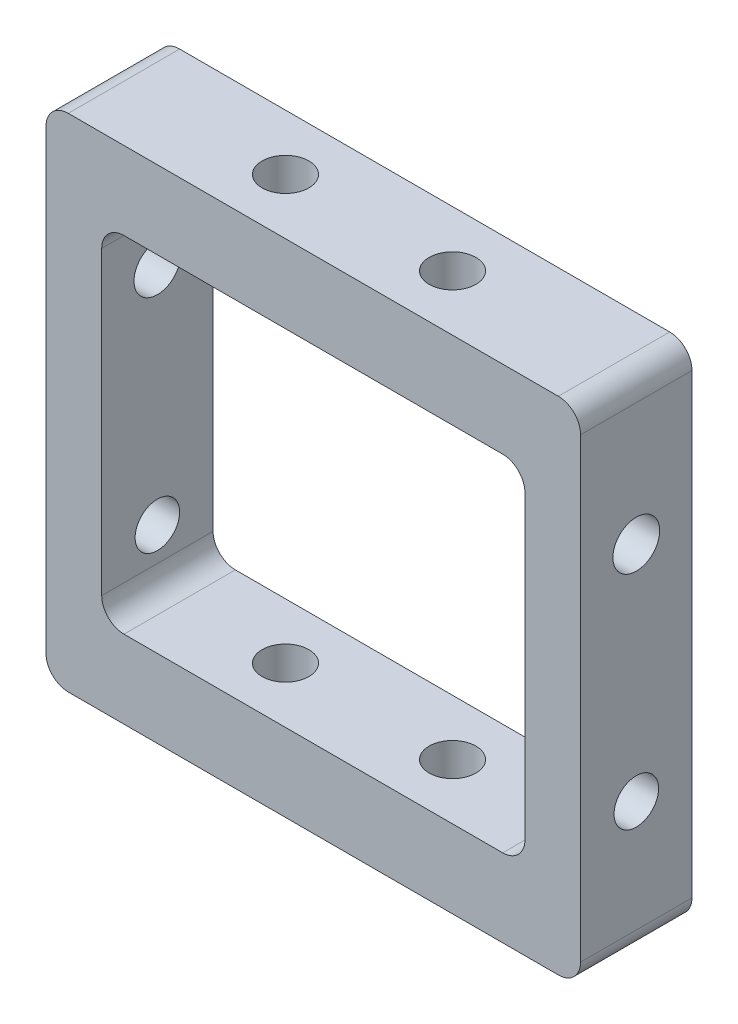
SolidWorks part; units mm, degrees
material "1060 合金"
ref_plane "前视基准面" through (0, 0, 0) normal (0, 0, 1) x (1, 0, 0)
ref_plane "上视基准面" through (0, 0, 0) normal (0, 1, 0) x (1, 0, 0)
ref_plane "右视基准面" through (0, 0, 0) normal (1, 0, 0) x (0, 0, -1)
sketch "草图1" plane through (0, 0, 0) normal (0, 0, 1) x (1, 0, 0)
  line L1 (-24, -22.5) -> (24, -22.5)
  line L2 (-24, -22.5) -> (-24, 22.5)
  line L3 (-24, 22.5) -> (24, 22.5)
  line L4 (24, -22.5) -> (24, 22.5)
  line L5 (-24, -22.5) -> (24, 22.5) construction
  line L6 (-24, 22.5) -> (24, -22.5) construction
  point P0 (0, 0)
  dimension "D1" = 45
  dimension "D2" = 48
extrude "凸台-拉伸1" add sketch "草图1" along normal blind 10
sketch "草图2" plane through (0, 22.5, 0) normal (0, 1, 0) x (1, 0, 0)
  line L0 (24, -5) -> (10, -5) construction
  line L1 (24, -10) -> (24, 0) construction
  line L2 (0, 0) -> (0, -13.6651) construction
  circle A0 centre (10, -5) radius 2.5
  circle A1 centre (-10, -5) radius 2.5
  dimension "D1" = 5
  dimension "D2" = 20
extrude "切除-拉伸1" cut sketch "草图2" against normal through all both and the other way through all
sketch "草图3" plane through (24, 0, 0) normal (1, 0, 0) x (0, 0, -1)
  line L0 (-5, -22.5) -> (-5, -10.5) construction
  line L1 (-10, -22.5) -> (0, -22.5) construction
  circle A0 centre (-5, -10.5) radius 2
  dimension "D1" = 4
  dimension "D2" = 12
extrude "切除-拉伸2" cut sketch "草图3" against normal through all
sketch "草图4" plane through (24, 0, 0) normal (1, 0, 0) x (0, 0, -1)
  line L0 (-5, -10.5) -> (-5, 9.5) construction
  circle A0 centre (-5, 9.5) radius 1.75
  dimension "D2" = 3.5
  dimension "D1" = 20
extrude "切除-拉伸3" cut sketch "草图4" against normal through all both and the other way through all
sketch "草图5" plane through (0, 0, 10) normal (0, 0, 1) x (1, 0, 0)
  line L0 (-8.15, -8.5) -> (-12.15, -8.5) construction
  line L1 (-12.5, -8.5) -> (-24, -8.5) construction
  line L3 (-10.15, -8.5) -> (-10.15, -12.5) construction
  line L4 (-10.15, -12.5) -> (-7.5, -12.5) construction
  line L6 (-10.15, -10.5) -> (24, -10.5) construction
  line L7 (-12.15, 8.15) -> (-8.15, 8.15) construction
  line L9 (-10.15, 8.15) -> (-10.15, 10.85) construction
  line L10 (-10.15, 10.85) -> (-7.85, 10.85) construction
  line L12 (-10.15, 9.5) -> (24, 9.5) construction
  line L13 (24, -22.5) -> (24, 22.5) construction
  line L14 (12.15, 8.15) -> (7.85, 8.15) construction
  line L16 (10, 8.15) -> (10, 9.5) construction
  line L17 (12.5, -8.5) -> (9.85, -8.5) construction
  line L18 (9.85, -8.5) -> (9.85, -10.5) construction
  line L19 (9.85, -8.5) -> (7.2, -8.5) construction
  line L20 (-24, -22.5) -> (24, -22.5) construction
  line L21 (-19, -2) -> (-1.3, -2)
  line L22 (-19, -2) -> (-19, -19)
  line L23 (-19, -19) -> (-1.3, -19)
  line L24 (-1.3, -2) -> (-1.3, -19)
  line L25 (-19, -2) -> (-1.3, -19) construction
  line L26 (-19, -19) -> (-1.3, -2) construction
  line L28 (0, 0) -> (0, -22.5) construction
  line L29 (19, -2) -> (1.3, -2)
  line L30 (1.3, -2) -> (1.3, -19)
  line L31 (19, -19) -> (1.3, -19)
  line L32 (19, -2) -> (19, -19)
  line L33 (24, 9.5) -> (24, -10.5) construction
  line L34 (24, -0.5) -> (0, -0.5) construction
  line L35 (-19, 18) -> (-1.3, 18)
  line L36 (-1.3, 1) -> (-1.3, 18)
  line L37 (-19, 1) -> (-1.3, 1)
  line L38 (-19, 1) -> (-19, 18)
  line L39 (19, 1) -> (19, 18)
  line L40 (19, 18) -> (1.3, 18)
  line L41 (1.3, 1) -> (1.3, 18)
  line L42 (19, 1) -> (1.3, 1)
  line L43 (-24, 22.5) -> (-24, -22.5) construction
  dimension "D1" = 2.65
  dimension "D2" = 5
  dimension "D3" = 3.5
  dimension "D4" = 20
  dimension "D5" = 2.65
extrude "切除-拉伸4" cut sketch "草图5" against normal through all
sketch "草图6" plane through (0, 0, 10) normal (0, 0, 1) x (1, 0, 0)
  line L0 (-19, 18) -> (-19, 16.5)
  line L1 (-19, 16.5) -> (-1.3, 16.5)
  line L2 (-1.3, 16.5) -> (-1.3, 18)
  line L3 (-1.3, 18) -> (-19, 18)
  line L4 (24, 22.5) -> (-24, 22.5) construction
  line L5 (0, 0) -> (0, 22.5) construction
  line L6 (1.3, 16.5) -> (1.3, 18)
  line L7 (19, 16.5) -> (1.3, 16.5)
  line L8 (19, 18) -> (19, 16.5)
  line L9 (1.3, 18) -> (19, 18)
  line L10 (-19, 1) -> (-19, -1.5)
  line L11 (-19, -1.5) -> (-1.3, -1.5)
  line L12 (-1.3, -1.5) -> (-1.3, 1)
  line L13 (-1.3, 1) -> (-19, 1)
  line L14 (1.3, -1.5) -> (1.3, 1)
  line L15 (19, -1.5) -> (1.3, -1.5)
  line L16 (19, 1) -> (19, -1.5)
  line L17 (1.3, 1) -> (19, 1)
  dimension "D1" = 6
  dimension "D2" = 2.5
extrude "切除-拉伸5" cut sketch "草图6" against normal through all
sketch "草图8" plane through (0, 22.5, 0) normal (0, 1, 0) x (1, 0, 0)
  circle A0 centre (10, -5) radius 2.5 construction
  circle A1 centre (-10, -5) radius 2.5 construction
  circle A2 centre (10, -5) radius 2.5
  circle A3 centre (-10, -5) radius 2.5
extrude "凸台-拉伸2" add sketch "草图8" against normal up to surface (45 mm away) up to face at (10, -22.5, 7.5)
sketch "草图10" plane through (0, 22.5, 0) normal (0, 1, 0) x (1, 0, 0)
  line L0 (0, 0) -> (0, -10) construction
  line L1 (24, 0) -> (-24, 0) construction
  line L2 (24, -10) -> (-24, -10) construction
  line L3 (-24, -5) -> (0, -5) construction
  line L4 (-24, -10) -> (-24, 0) construction
  circle A0 centre (-7.5, -5) radius 1.75
  circle A1 centre (7.5, -5) radius 1.75
  dimension "D1" = 3.5
  dimension "D2" = 15
extrude "切除-拉伸8" cut sketch "草图10" against normal up to surface (45 mm away) up to face at (0, -22.5, 5)
sketch "草图16" plane through (0, 0, 10) normal (0, 0, 1) x (1, 0, 0)
  line L0 (19, 18) -> (-19, 18)
  line L1 (-1.3, 18) -> (-19, 18) construction
  line L2 (-19, 18) -> (-19, -1.5) construction
  line L3 (-19, 18) -> (-19, -19)
  line L4 (-19, -19) -> (19, -19)
  line L5 (19, -19) -> (19, 18)
  line L6 (19, -1.5) -> (19, 18) construction
extrude "切除-拉伸13" cut sketch "草图16" against normal through all contours L0 L3 L4 L5
sketch "草图17" plane through (0, -19, 0) normal (0, 1, 0) x (1, 0, 0)
  line L4 (-19, -10) -> (19, -10)
  line L5 (19, -10) -> (19, 0)
  line L6 (19, 0) -> (-19, 0)
  line L7 (-19, 0) -> (-19, -10)
  line L8 (-19, -10) -> (19, -10)
  line L9 (19, -10) -> (19, 0)
  line L10 (19, 0) -> (-19, 0)
  line L11 (-19, 0) -> (-19, -10)
  circle A0 centre (7.5, -5) radius 1.75 construction
  circle A1 centre (-7.5, -5) radius 1.75 construction
  circle A2 centre (7.5, -5) radius 1.75
  circle A3 centre (-7.5, -5) radius 1.75
  dimension "D1" = 0
extrude "凸台-拉伸4" add sketch "草图17" along normal blind 3.5
sketch "草图18" plane through (0, 18, 0) normal (0, -1, 0) x (1, 0, 0)
  line L4 (19, 10) -> (-19, 10)
  line L5 (-19, 10) -> (-19, 0)
  line L6 (-19, 0) -> (19, 0)
  line L7 (19, 0) -> (19, 10)
  line L8 (19, 10) -> (-19, 10)
  line L9 (-19, 10) -> (-19, 0)
  line L10 (-19, 0) -> (19, 0)
  line L11 (19, 0) -> (19, 10)
  circle A0 centre (-7.5, 5) radius 1.75 construction
  circle A1 centre (7.5, 5) radius 1.75 construction
  circle A2 centre (-7.5, 5) radius 1.75
  circle A3 centre (7.5, 5) radius 1.75
  dimension "D1" = 0
extrude "凸台-拉伸5" add sketch "草图18" along normal blind 2.5
fillet "圆角2" radius 2 4 edges at (-19, -15.5, 5) (19, -15.5, 5) (19, 15.5, 5) (-19, 15.5, 5)
hole_wizard "M5 螺纹孔的螺纹孔钻头2" positions "草图21" profile "草图22" hole size "M5" standard "GB" end condition up to next
sketch "草图21" plane through (0, 22.5, 0) normal (0, 1, 0) x (1, 0, 0)
  point P0 (-7.5, -5)
  point P3 (7.5, -5)
sketch "草图22" plane through (-7.5, 22.5, 5) normal (1, 0, 0) x (0, 0, 1)
  line L0 (0, 0) -> (0, 45)
  line L1 (0, 45) -> (2.1, 45)
  line L2 (2.1, 45) -> (2.1, 0)
  line L5 (2.1, 0) -> (0, 0)
  line L11 (0, -6.35) -> (0, 107.95) construction
  dimension "通孔孔直径" = 4.2
  dimension "通孔孔深度" = 45
cosmetic thread "装饰螺纹线1" parameters "D2"=5
cosmetic thread "装饰螺纹线2" parameters "D2"=5
hole_wizard "M5 螺纹孔的螺纹孔钻头3" positions "草图23" profile "草图24" hole size "M5" standard "GB" end condition up to next
sketch "草图23" plane through (24, 0, 0) normal (1, 0, 0) x (0, 0, -1)
  point P0 (-5, 9.5)
sketch "草图24" plane through (24, 9.5, 5) normal (0, 1, 0) x (0, 0, -1)
  line L0 (0, 0) -> (0, 48)
  line L1 (0, 48) -> (2.1, 48)
  line L2 (2.1, 48) -> (2.1, 0)
  line L5 (2.1, 0) -> (0, 0)
  line L11 (0, -6.35) -> (0, 107.95) construction
  dimension "通孔孔直径" = 4.2
  dimension "通孔孔深度" = 48
cosmetic thread "装饰螺纹线3" parameters "D2"=5
fillet "圆角3" radius 2 4 edges at (24, -22.5, 5) (-24, -22.5, 5) (24, 22.5, 5) (-24, 22.5, 5)
